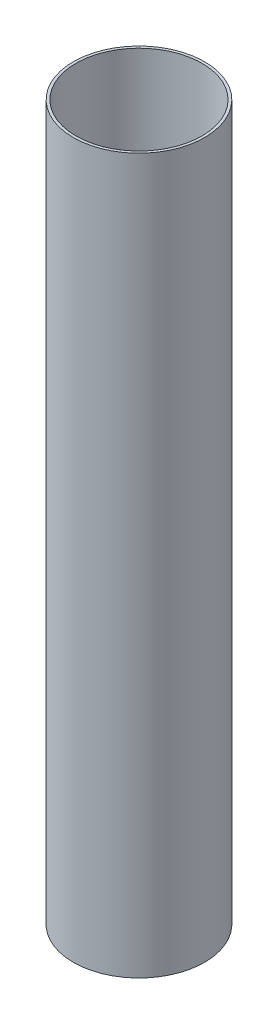
SolidWorks part; units mm, degrees
ref_plane "Front Plane" through (0, 0, 0) normal (0, 0, 1) x (1, 0, 0)
ref_plane "Top Plane" through (0, 0, 0) normal (0, 1, 0) x (1, 0, 0)
ref_plane "Right Plane" through (0, 0, 0) normal (1, 0, 0) x (0, 0, -1)
sketch "Sketch1" plane through (0, 0, 0) normal (0, 1, 0) x (1, 0, 0)
  circle A0 centre (0, 0) radius 39.7
  circle A1 centre (0, 0) radius 38.1
  dimension "D1" = 76.2
  dimension "D2" = 79.4
extrude "Boss-Extrude1" add sketch "Sketch1" along normal blind 431.8
